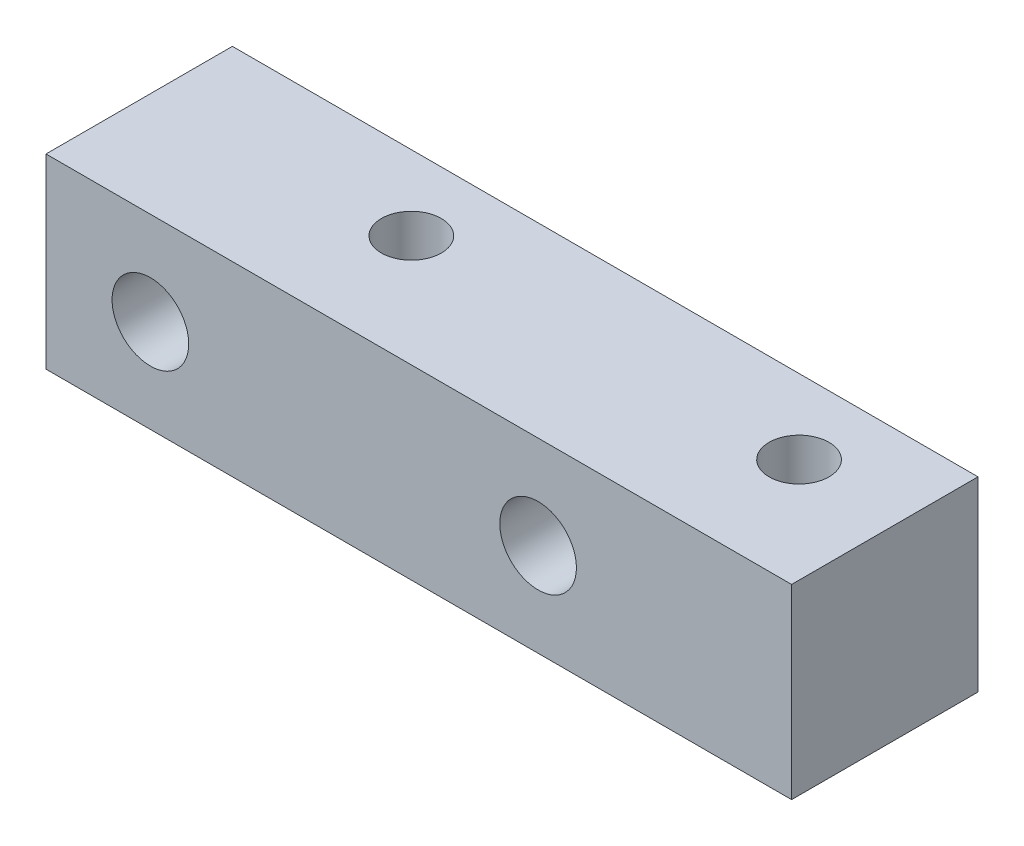
SolidWorks part; units mm, degrees
ref_plane "Front Plane" through (0, 0, 0) normal (0, 0, 1) x (1, 0, 0)
ref_plane "Top Plane" through (0, 0, 0) normal (0, 1, 0) x (1, 0, 0)
ref_plane "Right Plane" through (0, 0, 0) normal (1, 0, 0) x (0, 0, -1)
sketch "Sketch2" plane through (0, 0, 0) normal (0, 1, 0) x (1, 0, 0)
  line L1 (-31.75, 7.9375) -> (31.75, 7.9375)
  line L2 (-31.75, 7.9375) -> (-31.75, -7.9375)
  line L3 (-31.75, -7.9375) -> (31.75, -7.9375)
  line L4 (31.75, 7.9375) -> (31.75, -7.9375)
  line L5 (-31.75, 7.9375) -> (31.75, -7.9375) construction
  line L6 (-31.75, -7.9375) -> (31.75, 7.9375) construction
  point P0 (0, 0)
  dimension "D1" = 63.5
  dimension "D2" = 15.875
extrude "Boss-Extrude1" add sketch "Sketch2" against normal blind 15.875
sketch "Sketch4" plane through (0, 0, 0) normal (0, 1, 0) x (1, 0, 0)
  line L0 (-31.75, 1.5875) -> (31.75, 1.5875) construction
  line L2 (-31.75, 7.9375) -> (-31.75, -7.9375) construction
  line L5 (-31.75, -7.9375) -> (31.75, -7.9375) construction
  line L10 (31.75, -7.9375) -> (31.75, 7.9375) construction
  circle A0 centre (-10.16, 1.5875) radius 2.921
  circle A1 centre (22.86, 1.5875) radius 2.921
  dimension "D2" = 5.842
  dimension "D3" = 5.842
  dimension "D1" = 33.02
  dimension "D4" = 8.89
  dimension "D5" = 9.525
sketch "Sketch5" plane through (0, 0, 7.9375) normal (0, 0, 1) x (1, 0, 0)
  line L0 (-31.75, -7.9375) -> (31.75, -7.9375) construction
  line L1 (31.75, -15.875) -> (31.75, 0) construction
  line L2 (-31.75, -15.875) -> (-31.75, 0) construction
  circle A0 centre (10.16, -7.9375) radius 2.921
  circle A1 centre (-22.86, -7.9375) radius 2.921
  point P11 (-31.75, -7.9375)
  point P20 (-22.86, -7.9375)
  dimension "D4" = 8.89
  dimension "D1" = 33.02
hole_wizard "1/4-20 Tapped Hole" positions "Sketch13" profile "Sketch14" tap size "1/4-20" standard "ANSI Inch" end condition through all
sketch "Sketch13" plane through (0, 0, 0) normal (0, 1, 0) x (1, 0, 0)
  point P0 (-10.16, 1.5875)
  point P3 (22.86, 1.5875)
sketch "Sketch14" plane through (-10.16, 0, -1.5875) normal (1, 0, 0) x (0, 0, 1)
  line L0 (0, 0) -> (0, 15.875)
  line L1 (0, 15.875) -> (2.5527, 15.875)
  line L2 (2.5527, 15.875) -> (2.5527, 0)
  line L5 (2.5527, 0) -> (0, 0)
  line L11 (0, -6.35) -> (0, 107.95) construction
  dimension "Thru Tap Drill Dia." = 5.1054
  dimension "Thru Tap Drill Depth" = 15.875
cosmetic thread "Hole Thread3" parameters "D2"=6.35
cosmetic thread "Hole Thread4" parameters "D2"=6.35
hole_wizard "1/4 Clearance Hole" positions "Sketch15" profile "Sketch16" hole size "1/4" standard "ANSI Inch" end condition through all
sketch "Sketch15" plane through (0, 0, 7.9375) normal (0, 0, 1) x (1, 0, 0)
  point P0 (-22.86, -7.9375)
  point P3 (10.16, -7.9375)
sketch "Sketch16" plane through (-22.86, -7.9375, 7.9375) normal (1, 0, 0) x (0, -1, 0)
  line L0 (0, 0) -> (0, 15.875)
  line L1 (0, 15.875) -> (3.2639, 15.875)
  line L2 (3.2639, 15.875) -> (3.2639, 0)
  line L5 (3.2639, 0) -> (0, 0)
  line L11 (0, -6.35) -> (0, 107.95) construction
  dimension "Thru Hole Dia." = 6.5278
  dimension "Thru Hole Depth" = 15.875
